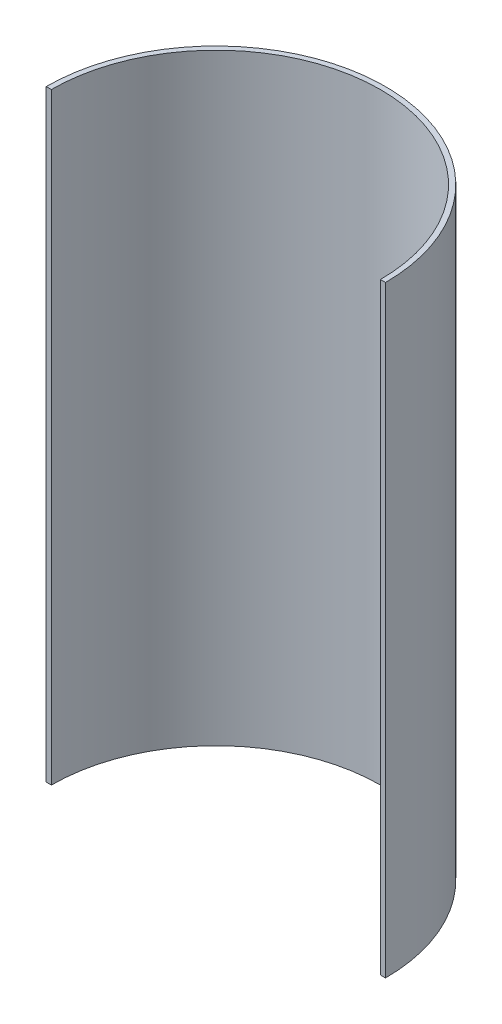
SolidWorks part; units mm, degrees
ref_plane "Front Plane" through (0, 0, 0) normal (0, 0, 1) x (1, 0, 0)
ref_plane "Top Plane" through (0, 0, 0) normal (0, 1, 0) x (1, 0, 0)
ref_plane "Right Plane" through (0, 0, 0) normal (1, 0, 0) x (0, 0, -1)
sketch "Sketch1" plane through (0, 0, 0) normal (0, 1, 0) x (1, 0, 0)
  line L0 (-4, 0) -> (4, 0)
  line L1 (525.5, 0) -> (517.5, 0)
  arc A0 (0, 0) -> (521.5, 0) centre (260.75, 0) cw construction
  arc A1 (4, 0) -> (517.5, 0) centre (260.75, 0) cw
  arc A2 (-4, 0) -> (525.5, 0) centre (260.75, 0) cw
  dimension "D1" = 260.75
  dimension "D2" = 4
  dimension "D3" = 4
extrude "Boss-Extrude1" add sketch "Sketch1" along normal blind 940
sketch "Sketch2" plane through (0, 0, 0) normal (0, 0, 1) x (1, 0, 0)
  line L0 (12.5, 0) -> (-12.5, 0)
  line L1 (2, 25) -> (2, 5)
  line L2 (0, 57.2935) -> (0, -51.2232) construction
  line L3 (-12.5, 0) -> (-12.5, 25)
  line L4 (-12.5, 25) -> (-2, 25)
  line L5 (-2, 25) -> (-2, 5)
  line L6 (-2, 5) -> (2, 5)
  line L8 (12.5, 25) -> (2, 25)
  line L9 (12.5, 0) -> (12.5, 25)
  point P11 (0, 5)
  point P14 (0, 0)
  dimension "D1" = 12.5
  dimension "D2" = 25
  dimension "D3" = 2
  dimension "D4" = 20
